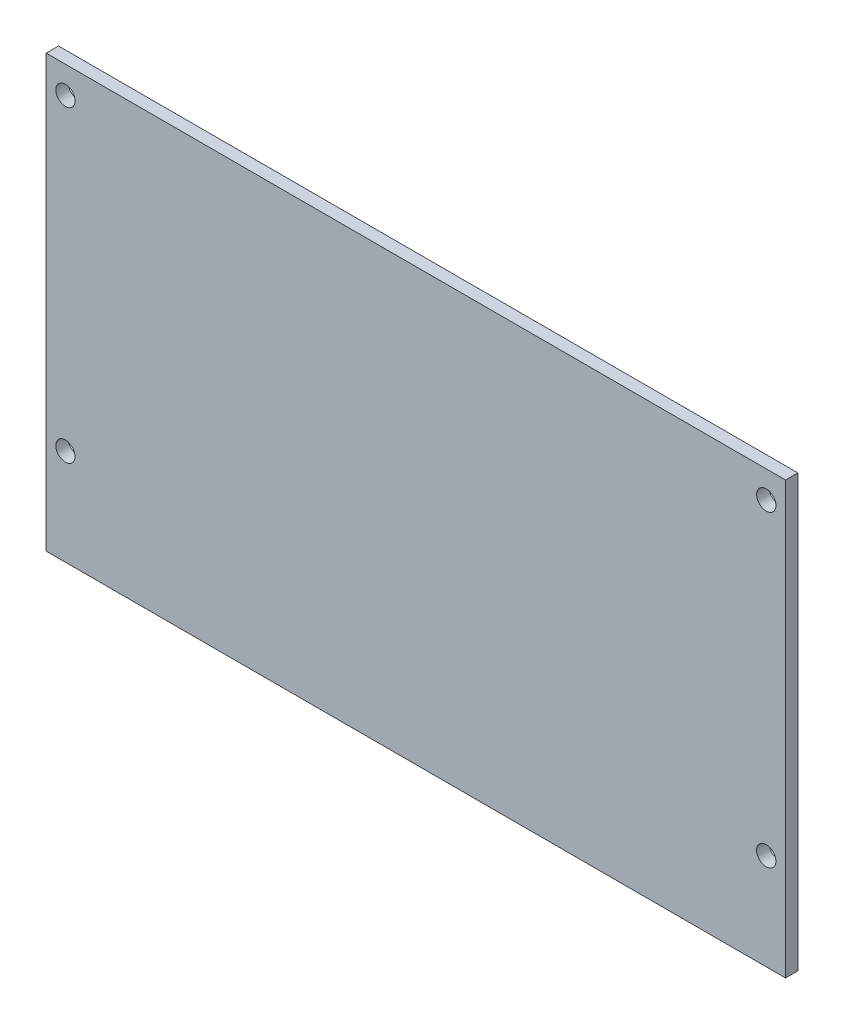
SolidWorks part; units mm, degrees
material "A-Glass Fiber"
ref_plane "Front Plane" through (0, 0, 0) normal (0, 0, 1) x (1, 0, 0)
ref_plane "Top Plane" through (0, 0, 0) normal (0, 1, 0) x (1, 0, 0)
ref_plane "Right Plane" through (0, 0, 0) normal (1, 0, 0) x (0, 0, -1)
sketch "Sketch1" plane through (0, 0, 0) normal (0, 0, 1) x (1, 0, 0)
  line L0 (0, 0) -> (0, 40.0445) construction
  line L1 (48, 28) -> (-48, 28)
  line L2 (48, 28) -> (48, -28)
  line L3 (48, -28) -> (-48, -28)
  line L4 (-48, 28) -> (-48, -28)
  line L5 (48, 28) -> (-48, -28) construction
  line L6 (48, -28) -> (-48, 28) construction
  line L7 (-45.5, 24.5) -> (-45.5, -15.5) construction
  circle A0 centre (-45.5, 24.5) radius 1.25
  circle A1 centre (-45.5, -15.5) radius 1.25
  circle A2 centre (45.5, -15.5) radius 1.25
  circle A3 centre (45.5, 24.5) radius 1.25
  point P0 (0, 0)
  dimension "D3" = 3.5
  dimension "D4" = 40
  dimension "D5" = 2.5
  dimension "D1" = 56
  dimension "D2" = 96
  dimension "D6" = 2.5
extrude "Boss-Extrude1" add sketch "Sketch1" along normal blind 1.6
